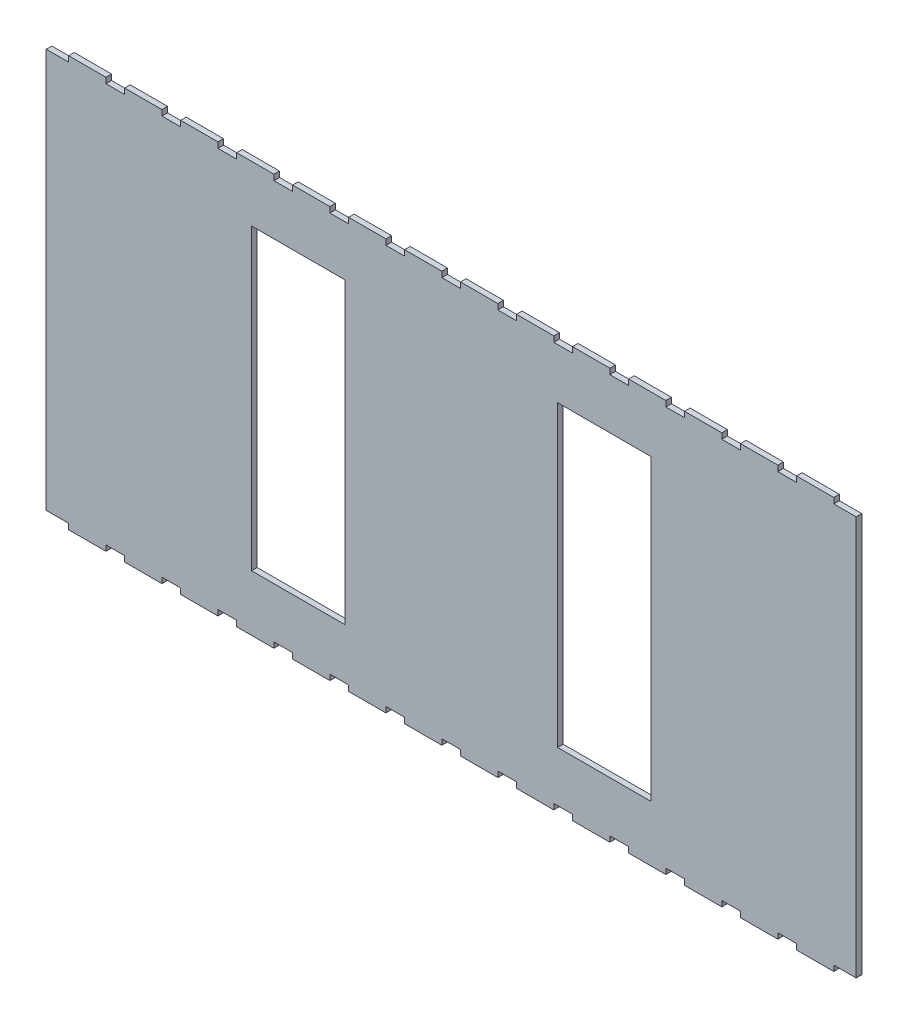
SolidWorks part; units mm, degrees
ref_plane "Plan de face" through (0, 0, 0) normal (0, 0, 1) x (1, 0, 0)
ref_plane "Plan de dessus" through (0, 0, 0) normal (0, 1, 0) x (1, 0, 0)
ref_plane "Plan de droite" through (0, 0, 0) normal (1, 0, 0) x (0, 0, -1)
sketch "Esquisse1" plane through (0, 0, 0) normal (0, 0, 1) x (1, 0, 0)
  line L1 (-217, 110) -> (217, 110)
  line L2 (-217, 110) -> (-217, -110)
  line L3 (-217, -110) -> (217, -110)
  line L4 (217, 110) -> (217, -110)
  line L5 (-217, 110) -> (217, -110) construction
  line L6 (-217, -110) -> (217, 110) construction
  point P0 (0, 0)
  dimension "D1" = 434
  dimension "D2" = 220
extrude "Boss.-Extru.1" add sketch "Esquisse1" along normal blind 3
sketch "Esquisse2" plane through (0, 0, 3) normal (0, 0, 1) x (1, 0, 0)
  line L0 (-217, 0) -> (217, 0) construction
  line L1 (-217, 110) -> (-217, -110) construction
  line L2 (217, -110) -> (217, 110) construction
  line L3 (217, 110) -> (-217, 110) construction
  line L4 (-215, 110) -> (-205, 110)
  line L5 (-215, 110) -> (-215, 107)
  line L6 (-215, 107) -> (-205, 107)
  line L7 (-205, 110) -> (-205, 107)
  line L8 (-185, 110) -> (-185, 107)
  line L9 (-185, 110) -> (-175, 110)
  line L10 (-175, 110) -> (-175, 107)
  line L11 (-185, 107) -> (-175, 107)
  line L12 (-155, 110) -> (-155, 107)
  line L13 (-155, 110) -> (-145, 110)
  line L14 (-145, 110) -> (-145, 107)
  line L15 (-155, 107) -> (-145, 107)
  line L16 (-125, 110) -> (-125, 107)
  line L17 (-125, 110) -> (-115, 110)
  line L18 (-115, 110) -> (-115, 107)
  line L19 (-125, 107) -> (-115, 107)
  line L20 (-95, 110) -> (-95, 107)
  line L21 (-95, 110) -> (-85, 110)
  line L22 (-85, 110) -> (-85, 107)
  line L23 (-95, 107) -> (-85, 107)
  line L24 (-65, 110) -> (-65, 107)
  line L25 (-65, 110) -> (-55, 110)
  line L26 (-55, 110) -> (-55, 107)
  line L27 (-65, 107) -> (-55, 107)
  line L28 (-35, 110) -> (-35, 107)
  line L29 (-35, 110) -> (-25, 110)
  line L30 (-25, 110) -> (-25, 107)
  line L31 (-35, 107) -> (-25, 107)
  line L32 (-5, 110) -> (-5, 107)
  line L33 (-5, 110) -> (5, 110)
  line L34 (5, 110) -> (5, 107)
  line L35 (-5, 107) -> (5, 107)
  line L36 (25, 110) -> (25, 107)
  line L37 (25, 110) -> (35, 110)
  line L38 (35, 110) -> (35, 107)
  line L39 (25, 107) -> (35, 107)
  line L40 (55, 110) -> (55, 107)
  line L41 (55, 110) -> (65, 110)
  line L42 (65, 110) -> (65, 107)
  line L43 (55, 107) -> (65, 107)
  line L44 (85, 110) -> (85, 107)
  line L45 (85, 110) -> (95, 110)
  line L46 (95, 110) -> (95, 107)
  line L47 (85, 107) -> (95, 107)
  line L48 (115, 110) -> (115, 107)
  line L49 (115, 110) -> (125, 110)
  line L50 (125, 110) -> (125, 107)
  line L51 (115, 107) -> (125, 107)
  line L52 (145, 110) -> (145, 107)
  line L53 (145, 110) -> (155, 110)
  line L54 (155, 110) -> (155, 107)
  line L55 (145, 107) -> (155, 107)
  line L56 (175, 110) -> (175, 107)
  line L57 (175, 110) -> (185, 110)
  line L58 (185, 110) -> (185, 107)
  line L59 (175, 107) -> (185, 107)
  line L60 (205, 110) -> (205, 107)
  line L61 (205, 110) -> (215, 110)
  line L62 (215, 110) -> (215, 107)
  line L63 (205, 107) -> (215, 107)
  line L192 (205, -107) -> (215, -107)
  line L193 (215, -110) -> (215, -107)
  line L194 (205, -110) -> (215, -110)
  line L195 (205, -110) -> (205, -107)
  line L196 (175, -107) -> (185, -107)
  line L197 (185, -110) -> (185, -107)
  line L198 (175, -110) -> (185, -110)
  line L199 (175, -110) -> (175, -107)
  line L200 (145, -107) -> (155, -107)
  line L201 (155, -110) -> (155, -107)
  line L202 (145, -110) -> (155, -110)
  line L203 (145, -110) -> (145, -107)
  line L204 (115, -107) -> (125, -107)
  line L205 (125, -110) -> (125, -107)
  line L206 (115, -110) -> (125, -110)
  line L207 (115, -110) -> (115, -107)
  line L208 (85, -107) -> (95, -107)
  line L209 (95, -110) -> (95, -107)
  line L210 (85, -110) -> (95, -110)
  line L211 (85, -110) -> (85, -107)
  line L212 (55, -107) -> (65, -107)
  line L213 (65, -110) -> (65, -107)
  line L214 (55, -110) -> (65, -110)
  line L215 (55, -110) -> (55, -107)
  line L216 (25, -107) -> (35, -107)
  line L217 (35, -110) -> (35, -107)
  line L218 (25, -110) -> (35, -110)
  line L219 (25, -110) -> (25, -107)
  line L220 (-5, -107) -> (5, -107)
  line L221 (5, -110) -> (5, -107)
  line L222 (-5, -110) -> (5, -110)
  line L223 (-5, -110) -> (-5, -107)
  line L224 (-35, -107) -> (-25, -107)
  line L225 (-25, -110) -> (-25, -107)
  line L226 (-35, -110) -> (-25, -110)
  line L227 (-35, -110) -> (-35, -107)
  line L228 (-65, -107) -> (-55, -107)
  line L229 (-55, -110) -> (-55, -107)
  line L230 (-65, -110) -> (-55, -110)
  line L231 (-65, -110) -> (-65, -107)
  line L232 (-95, -107) -> (-85, -107)
  line L233 (-85, -110) -> (-85, -107)
  line L234 (-95, -110) -> (-85, -110)
  line L235 (-95, -110) -> (-95, -107)
  line L236 (-125, -107) -> (-115, -107)
  line L237 (-115, -110) -> (-115, -107)
  line L238 (-125, -110) -> (-115, -110)
  line L239 (-125, -110) -> (-125, -107)
  line L240 (-155, -107) -> (-145, -107)
  line L241 (-145, -110) -> (-145, -107)
  line L242 (-155, -110) -> (-145, -110)
  line L243 (-155, -110) -> (-155, -107)
  line L244 (-185, -107) -> (-175, -107)
  line L245 (-175, -110) -> (-175, -107)
  line L246 (-185, -110) -> (-175, -110)
  line L247 (-185, -110) -> (-185, -107)
  line L248 (-205, -110) -> (-205, -107)
  line L249 (-215, -107) -> (-205, -107)
  line L250 (-215, -110) -> (-215, -107)
  line L251 (-215, -110) -> (-205, -110)
  line L253 (-217, 110) -> (-215, 110)
  line L254 (-217, 110) -> (-217, 107)
  line L255 (-217, 107) -> (-215, 107)
  line L256 (-215, 110) -> (-215, 107)
  line L257 (215, 110) -> (217, 110)
  line L258 (215, 110) -> (215, 107)
  line L259 (215, 107) -> (217, 107)
  line L260 (217, 110) -> (217, 107)
  line L261 (-217, -110) -> (-215, -110)
  line L262 (-217, -110) -> (-217, -107)
  line L263 (-217, -107) -> (-215, -107)
  line L264 (-215, -110) -> (-215, -107)
  line L265 (215, -107) -> (217, -107)
  line L266 (215, -107) -> (215, -110)
  line L267 (215, -110) -> (217, -110)
  line L268 (217, -107) -> (217, -110)
  line M127 (217, 110) -> (-217, 110)
  line M128 (-217, 110) -> (-217, -110)
  line M129 (-217, -110) -> (217, -110)
  dimension "D1" = 3
  dimension "D2" = 10
  dimension "D3" = 2
  dimension "D5" = 20
  dimension "D4" = 15
extrude "Enlèv. mat.-Extru.1" cut sketch "Esquisse2" against normal blind 3 contours L7 L5 L6 M127 | L8 L11 L10 M127 | L12 L15 L14 M127 | L16 L19 L18 M127 | L20 L23 L22 M127 | L28 L31 L30 M127 | L36 L39 L38 M127 | L40 L43 L42 M127 | L44 L47 L46 M127 | L48 L51 L50 M127 | L52 L55 L54 M127 | L56 L59 L58 M127 | L60 L63 L62 M127 | L195 L193 L192 M129 | L199 L197 L196 M129 | L203 L201 L200 M129 | L211 L209 L208 M129 | L215 L213 L212 M129 | L227 L225 L224 M129 | L231 L229 L228 M129 | L235 L233 L232 M129 | L239 L237 L236 M129 | L243 L241 L240 M129 | L250 L248 L249 M129 | L247 L245 L244 M129 | L263 L250 M128 M129 | L255 L5 M128 M127 | L25 L26 L27 L24 | L33 L34 L35 L32 | L204 L205 L206 L207 | L216 L217 L218 L219 | L220 L221 L222 L223 | L258 L257 L260 L259 | L266 L265 L268 L267
sketch "Esquisse3" plane through (0, 0, 3) normal (0, 0, 1) x (1, 0, 0)
  line L0 (0, 122.6824) -> (0, -129.993) construction
  line L1 (-185, 110) -> (-205, 110) construction
  line L2 (-107, 80) -> (-57, 80)
  line L3 (-107, 80) -> (-107, -80)
  line L4 (-107, -80) -> (-57, -80)
  line L5 (-57, 80) -> (-57, -80)
  line L6 (-205, -110) -> (-185, -110) construction
  line L7 (-217, 107) -> (-217, -107) construction
  line L8 (107, -80) -> (57, -80)
  line L9 (57, 80) -> (57, -80)
  line L10 (107, 80) -> (57, 80)
  line L11 (107, 80) -> (107, -80)
  point P9 (-195, 110)
  dimension "D1" = 50
  dimension "D2" = 30
  dimension "D3" = 30
  dimension "D4" = 110
extrude "Enlèv. mat.-Extru.2" cut sketch "Esquisse3" against normal blind 3 contours L3 L2 L5 L4 | L8 L9 L10 L11
